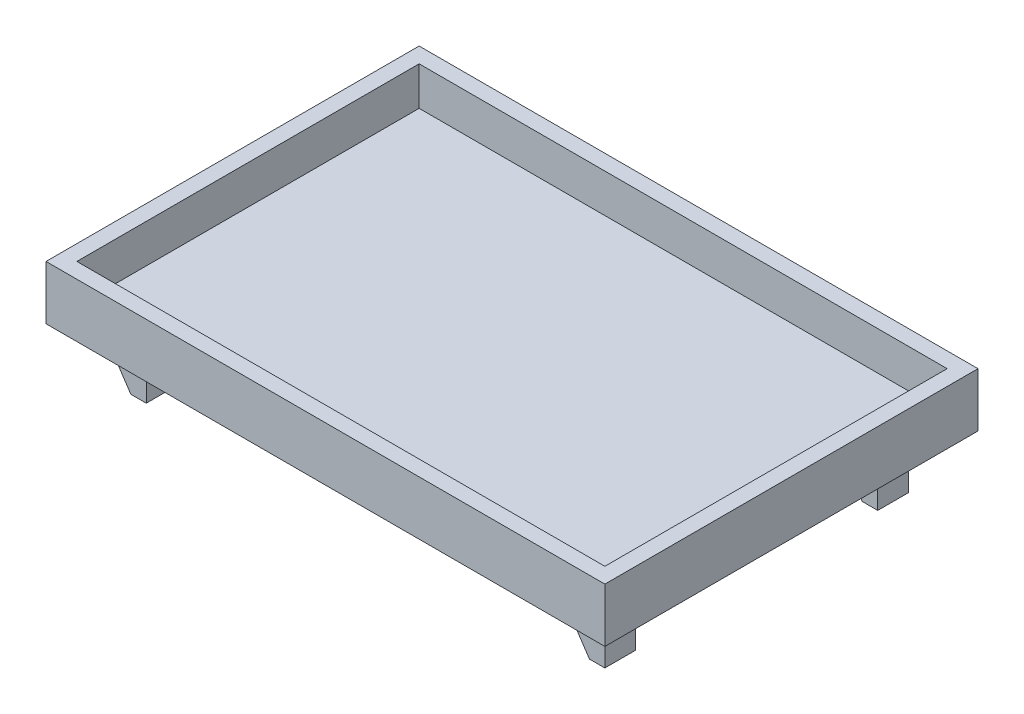
SolidWorks part; units mm, degrees
ref_plane "Front Plane" through (0, 0, 0) normal (0, 0, 1) x (1, 0, 0)
ref_plane "Top Plane" through (0, 0, 0) normal (0, 1, 0) x (1, 0, 0)
ref_plane "Right Plane" through (0, 0, 0) normal (1, 0, 0) x (0, 0, -1)
sketch "Sketch1" plane through (0, 0, 0) normal (0, 1, 0) x (1, 0, 0)
  line L0 (46.0121, -30.7213) -> (46.0121, 30.7213)
  line L1 (43.4721, -28.1813) -> (-43.4721, -28.1813) construction
  line L2 (43.4721, -28.1813) -> (43.4721, 28.1813) construction
  line L3 (43.4721, 28.1813) -> (-43.4721, 28.1813) construction
  line L4 (-43.4721, -28.1813) -> (-43.4721, 28.1813) construction
  line L5 (43.4721, -28.1813) -> (-43.4721, 28.1813) construction
  line L6 (43.4721, 28.1813) -> (-43.4721, -28.1813) construction
  line L7 (46.0121, 30.7213) -> (-46.0121, 30.7213)
  line L8 (-46.0121, -30.7213) -> (-46.0121, 30.7213)
  line L9 (46.0121, -30.7213) -> (-46.0121, -30.7213)
  point P0 (0, 0)
  dimension "D1" = 56.3626
  dimension "D2" = 86.9442
  dimension "D3" = 2.54
extrude "Boss-Extrude1" add sketch "Sketch1" against normal blind 8.89
sketch "Sketch2" plane through (0, 0, 0) normal (0, 1, 0) x (1, 0, 0)
  line L35 (-43.4721, -28.1813) -> (43.4721, -28.1813)
  line L36 (-43.4721, -28.1813) -> (-43.4721, 28.1813)
  line L37 (-43.4721, 28.1813) -> (43.4721, 28.1813)
  line L42 (43.4721, -28.1813) -> (43.4721, 28.1813)
  line L43 (-43.4721, -28.1813) -> (43.4721, 28.1813) construction
  line L44 (-43.4721, 28.1813) -> (43.4721, -28.1813) construction
  point P0 (0, 0)
  dimension "D1" = 56.3626
  dimension "D2" = 86.9442
extrude "Cut-Extrude4" cut sketch "Sketch2" against normal blind 6.35
sketch "Sketch3" plane through (0, -8.89, 0) normal (0, -1, 0) x (1, 0, 0)
  line L12 (43.4721, 28.1813) -> (-43.4721, 28.1813) construction
  line L13 (-43.4721, 28.1813) -> (-43.4721, -28.1813) construction
  line L14 (0, -30.7213) -> (0, 30.7213) construction
  line L19 (-46.0121, 30.7213) -> (46.0121, 30.7213) construction
  line L20 (-43.4721, -28.1813) -> (43.4721, -28.1813) construction
  line L21 (43.4721, -28.1813) -> (43.4721, 28.1813) construction
  line L22 (40.2971, 25.0063) -> (-40.2971, 25.0063) construction
  line L23 (-40.2971, 25.0063) -> (-40.2971, -25.0063) construction
  line L24 (46.0121, 30.7213) -> (-46.0121, 30.7213)
  line L25 (-46.0121, 30.7213) -> (-46.0121, -30.7213)
  line L26 (-46.0121, -30.7213) -> (46.0121, -30.7213)
  line L27 (46.0121, -30.7213) -> (46.0121, 30.7213)
  line L28 (46.0121, 30.7213) -> (-46.0121, 30.7213) construction
  line L29 (-46.0121, 30.7213) -> (-46.0121, -30.7213) construction
  line L30 (-46.0121, -30.7213) -> (46.0121, -30.7213) construction
  line L31 (46.0121, -30.7213) -> (46.0121, 30.7213) construction
  line L32 (-40.2971, -25.0063) -> (40.2971, -25.0063) construction
  line L33 (40.2971, -25.0063) -> (40.2971, 25.0063) construction
  line L34 (40.2971, -19.9263) -> (35.2171, -19.9263)
  line L35 (-40.2971, 25.0063) -> (-35.2171, 25.0063)
  line L36 (-40.2971, 25.0063) -> (-40.2971, 19.9263)
  line L37 (-40.2971, 19.9263) -> (-35.2171, 19.9263)
  line L38 (-35.2171, 25.0063) -> (-35.2171, 19.9263)
  line L39 (-40.2971, -25.0063) -> (-35.2171, -25.0063)
  line L40 (-40.2971, -25.0063) -> (-40.2971, -19.9263)
  line L41 (-40.2971, -19.9263) -> (-35.2171, -19.9263)
  line L42 (-35.2171, -25.0063) -> (-35.2171, -19.9263)
  line L43 (35.2171, -25.0063) -> (35.2171, -19.9263)
  line L44 (40.2971, -25.0063) -> (35.2171, -25.0063)
  line L45 (40.2971, -25.0063) -> (40.2971, -19.9263)
  line L46 (40.2971, 19.9263) -> (35.2171, 19.9263)
  line L47 (35.2171, 25.0063) -> (35.2171, 19.9263)
  line L48 (40.2971, 25.0063) -> (35.2171, 25.0063)
  line L49 (40.2971, 25.0063) -> (40.2971, 19.9263)
  point P5 (0, 0)
  point P11 (0, 0)
  dimension "D1" = 0
  dimension "D2" = 2.54
  dimension "D3" = 3.175
  dimension "D4" = 5.08
extrude "Boss-Extrude2" add sketch "Sketch3" along normal blind 8.7884
sketch "Sketch4" plane through (0, 0, 25.0063) normal (0, 0, 1) x (1, 0, 0)
  line L1 (35.2171, -13.8769) -> (35.2171, -17.6784)
  line L2 (35.2171, -8.89) -> (35.2171, -12.6069)
  line L3 (-35.2171, -17.6784) -> (-40.2971, -17.6784) construction
  line L4 (-37.7571, -17.6784) -> (-40.2971, -13.8769)
  line L5 (-38.576, -12.0682) -> (-38.576, -8.89)
  line L6 (-40.2971, -17.6784) -> (-40.2971, -8.89) construction
  line L7 (35.2171, -17.6784) -> (37.7571, -17.6784)
  line L8 (-40.2971, -12.6069) -> (-38.576, -12.0682)
  line L9 (-46.0121, -8.89) -> (46.0121, -8.89) construction
  line L10 (-38.576, -8.89) -> (-40.2971, -8.89)
  line L11 (-40.2971, -8.89) -> (-40.2971, -12.6069)
  line L12 (-40.2971, -13.8769) -> (-40.2971, -17.6784)
  line L13 (-40.2971, -17.6784) -> (-37.7571, -17.6784)
  line L14 (36.9382, -12.0682) -> (36.9382, -8.89)
  line L15 (37.7571, -17.6784) -> (35.2171, -13.8769)
  line L16 (36.9382, -8.89) -> (35.2171, -8.89)
  line L17 (35.2171, -12.6069) -> (36.9382, -12.0682)
  dimension "D1" = 4.572
  dimension "D2" = 1.27
  dimension "D3" = 1.8034
  dimension "D4" = 4.572
  dimension "D5" = 1.27
  dimension "D6" = 1.8034
extrude "Cut-Extrude5" cut sketch "Sketch4" against normal up to next (5.08 mm away)
mirror "Mirror1" about plane through (0, 0, 0) normal (0, 0, 1) of "Cut-Extrude5"
